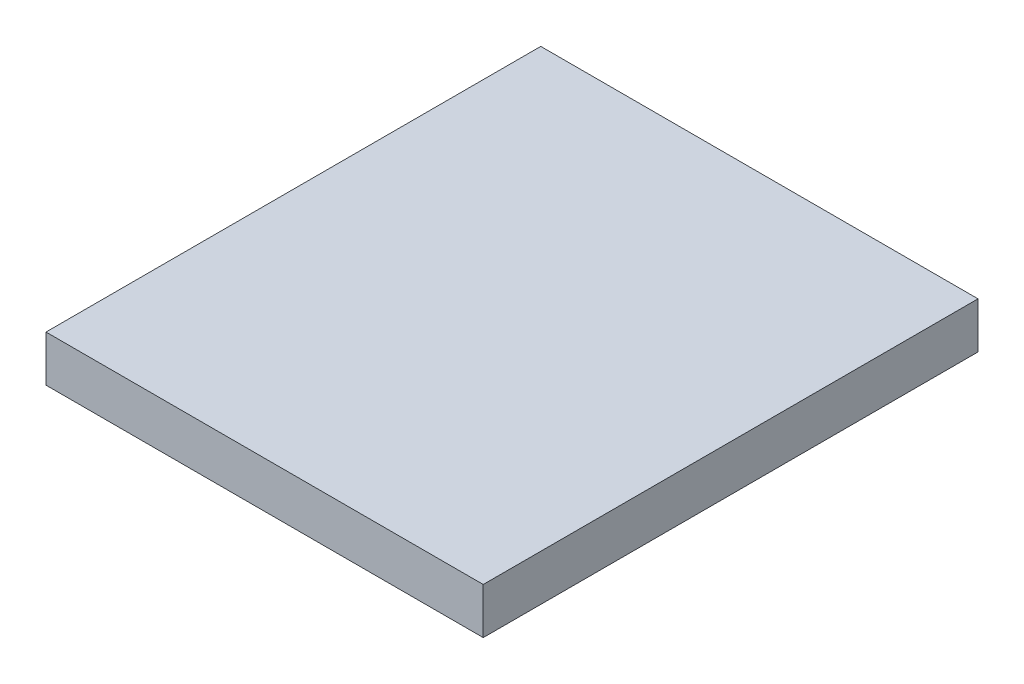
SolidWorks part; units mm, degrees
ref_plane "Front Plane" through (0, 0, 0) normal (0, 0, 1) x (1, 0, 0)
ref_plane "Top Plane" through (0, 0, 0) normal (0, 1, 0) x (1, 0, 0)
ref_plane "Right Plane" through (0, 0, 0) normal (1, 0, 0) x (0, 0, -1)
sketch "Sketch1" plane through (0, 0, 0) normal (0, 1, 0) x (1, 0, 0)
  line L0 (0, 0) -> (0, 43)
  line L1 (0, 43) -> (38, 43)
  line L2 (38, 43) -> (38, 0)
  line L3 (38, 0) -> (0, 0)
  dimension "D1" = 38
  dimension "D2" = 43
extrude "Boss-Extrude1" add sketch "Sketch1" along normal blind 4
